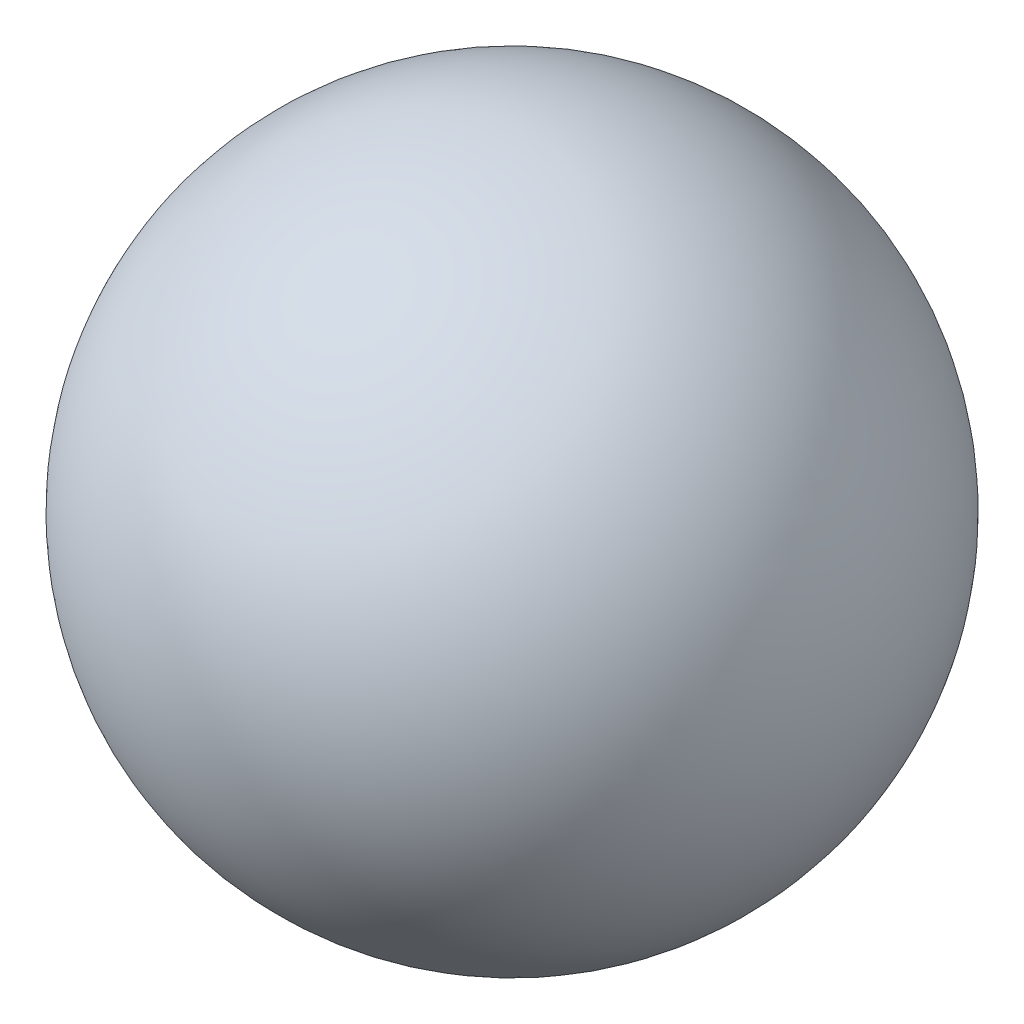
SolidWorks part; units mm, degrees
ref_plane "Front Plane" through (0, 0, 0) normal (0, 0, 1) x (1, 0, 0)
ref_plane "Top Plane" through (0, 0, 0) normal (0, 1, 0) x (1, 0, 0)
ref_plane "Right Plane" through (0, 0, 0) normal (1, 0, 0) x (0, 0, -1)
sketch "Sketch1" plane through (0, 0, 0) normal (0, 0, 1) x (1, 0, 0)
  line L0 (0, 0) -> (22.225, 0)
  line L1 (22.225, 0) -> (-22.225, 0)
  circle A0 centre (0, 0) radius 22.225
  dimension "D1" = 44.45
revolve "Revolve1" add sketch "Sketch1" angle 360 about L1
